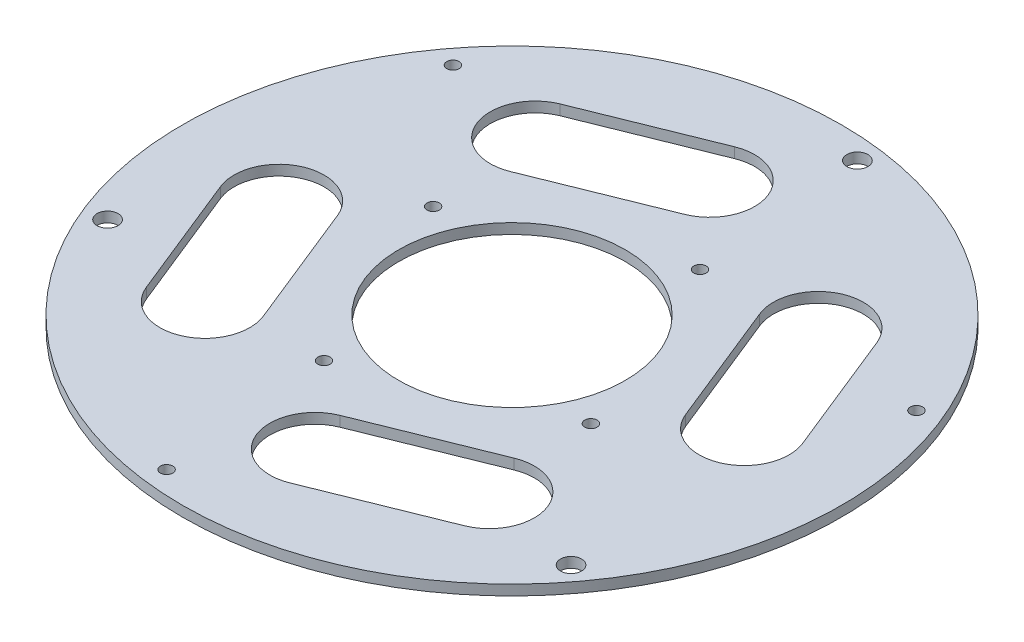
SolidWorks part; units mm, degrees
material "Aleación 1060"
ref_plane "Front Plane" through (0, 0, 0) normal (0, 0, 1) x (1, 0, 0)
ref_plane "Top Plane" through (0, 0, 0) normal (0, 1, 0) x (1, 0, 0)
ref_plane "Right Plane" through (0, 0, 0) normal (1, 0, 0) x (0, 0, -1)
sketch "Sketch1" plane through (0, 0, 0) normal (0, 1, 0) x (1, 0, 0)
  circle A0 centre (0, 0) radius 160
  circle A1 centre (0, 0) radius 55
  dimension "D1" = 0
extrude "Boss-Extrude1" add sketch "Sketch1" along normal blind 3
sketch "Sketch2" plane through (0, 3, 0) normal (0, 1, 0) x (1, 0, 0)
  circle A1 centre (0, 0) radius 70
  circle A2 centre (64.7949, -26.4882) radius 2.5
  dimension "D1" = 0
  dimension "D2" = 70
extrude "Cut-Extrude1" cut sketch "Sketch2" against normal blind 5 contours A2
pattern_circular "CirPattern1" count 4 over 360 about axis through (0, 0, 0) along (0, 1, 0) of "Cut-Extrude1"
sketch "Sketch3" plane through (0, 0, 0) normal (0, -1, 0) x (1, 0, 0)
  line L0 (64.7949, 26.4882) -> (26.4882, -64.7949)
  line L3 (45.6406, -19.1556) -> (138.3138, -58.0457)
  line L4 (138.3138, -58.0457) -> (64.7949, 26.4882)
  circle A0 centre (0, 0) radius 140
  circle A1 centre (138.3138, -58.0457) radius 5.1
  circle A2 centre (64.7949, 26.4882) radius 2.5 construction
  circle A6 centre (26.4882, -64.7949) radius 2.5 construction
  point P11 (45.6406, -19.1556)
  dimension "D1" = 0
  dimension "D2" = 10.2
  dimension "D4" = 0
  dimension "D14" = 150
  dimension "D3" = 0
  dimension "D5" = 0
  dimension "D6" = 0
  dimension "D7" = 0
  dimension "D8" = 49.495
  dimension "D9" = 0
  dimension "D10" = 0
  dimension "D11" = 0
  dimension "D12" = 90
  dimension "D13" = 0
extrude "Cut-Extrude3" cut sketch "Sketch3" against normal through all contours A0 A1 L4 L3 | L4 A1 L3
pattern_circular "CirPattern2" count 3 over 360 about axis through (0, 0, 0) along (0, 1, 0) of "Cut-Extrude3"
sketch "Sketch4" plane through (0, 3, 0) normal (0, 1, 0) x (1, 0, 0)
  line L0 (78.13, -76.3093) -> (-0.703, -108.0953) construction
  line L1 (87.4788, -99.4955) -> (8.6458, -131.2815)
  line L2 (68.7812, -53.1231) -> (-10.0519, -84.9091)
  arc A0 (87.4788, -99.4955) -> (68.7812, -53.1231) centre (78.13, -76.3093) ccw
  arc A1 (-10.0519, -84.9091) -> (8.6458, -131.2815) centre (-0.703, -108.0953) ccw
  point P2 (38.7135, -92.2023)
  dimension "D1" = 25
  dimension "D2" = 85
  dimension "D3" = 100
extrude "Cut-Extrude4" cut sketch "Sketch4" against normal through all
pattern_circular "CirPattern3" count 4 over 360 about axis through (0, 0, 0) along (0, 1, 0) of "Cut-Extrude4"
sketch "Sketch5" plane through (0, 3, 0) normal (0, 1, 0) x (1, 0, 0)
  circle A1 centre (0, 0) radius 160
extrude "Boss-Extrude2" add sketch "Sketch5" along normal blind 5 contours A1
sketch "Sketch6" plane through (0, 3, 0) normal (0, -1, 0) x (-1, 0, 0)
  circle A0 centre (-138.3138, 58.0457) radius 5.1
extrude "Cut-Extrude5" cut sketch "Sketch6" against normal blind 5
sketch "Sketch7" plane through (0, 3, 0) normal (0, -1, 0) x (-1, 0, 0)
  circle A0 centre (119.4259, 90.7604) radius 5.1
extrude "Cut-Extrude6" cut sketch "Sketch7" against normal blind 5
sketch "Sketch8" plane through (0, 3, 0) normal (0, -1, 0) x (-1, 0, 0)
  circle A0 centre (18.8878, -148.8061) radius 5.1
extrude "Cut-Extrude7" cut sketch "Sketch8" against normal blind 5
sketch "Sketch9" plane through (0, 3, 0) normal (0, -1, 0) x (-1, 0, 0)
  circle A0 centre (26.4882, -64.7949) radius 2.5
extrude "Cut-Extrude8" cut sketch "Sketch9" against normal blind 5
sketch "Sketch10" plane through (0, 3, 0) normal (0, -1, 0) x (-1, 0, 0)
  circle A0 centre (-64.7949, -26.4882) radius 2.5
extrude "Cut-Extrude9" cut sketch "Sketch10" against normal blind 5 contours A0
sketch "Sketch11" plane through (0, 3, 0) normal (0, -1, 0) x (-1, 0, 0)
  circle A0 centre (64.7949, 26.4882) radius 2.5
extrude "Cut-Extrude10" cut sketch "Sketch11" against normal blind 5 contours A0
sketch "Sketch12" plane through (0, 3, 0) normal (0, -1, 0) x (-1, 0, 0)
  circle A0 centre (-26.4882, 64.7949) radius 2.5
extrude "Cut-Extrude11" cut sketch "Sketch12" against normal blind 5
sketch "Sketch13" plane through (0, 3, 0) normal (0, -1, 0) x (-1, 0, 0)
  circle A1 centre (0, 0) radius 55
extrude "Cut-Extrude12" cut sketch "Sketch13" against normal blind 5
sketch "Sketch14" plane through (0, 3, 0) normal (0, -1, 0) x (-1, 0, 0)
  line L0 (16.7984, 124.7596) -> (77.0825, 100.4527)
  line L1 (-59.645, 60.6286) -> (-83.9519, 0.3445)
  line L4 (-100.1136, 77.0825) -> (-124.468, 16.6808)
  line L5 (84.291, -0.3445) -> (59.9367, -60.7462)
  line L6 (124.7596, -16.7984) -> (100.4527, -77.0825)
  line L7 (-115.3885, 48.0623) -> (-112.3145, 46.8228)
  line L8 (131.2815, -8.6458) -> (99.4955, -87.4788) construction
  line L9 (-69.0161, 29.3647) -> (-71.7985, 30.4865)
  line L10 (-53.1231, 68.7812) -> (-84.9091, -10.0519) construction
  line L11 (-131.2815, 8.6458) -> (-99.4955, 87.4788) construction
  line L12 (115.3885, -48.0623) -> (112.6062, -46.9404)
  line L13 (-48.0623, -115.3885) -> (-46.8228, -112.3145)
  line L14 (48.0623, 115.3885) -> (46.9404, 112.6062)
  line L15 (-29.3647, -69.0161) -> (-30.4865, -71.7985)
  line L16 (-77.0825, -100.1136) -> (-16.6808, -124.468)
  line L17 (-60.6286, -59.645) -> (-0.3445, -83.9519)
  line L18 (0.3445, 84.291) -> (60.7462, 59.9367)
  line L19 (48.0623, 115.3885) -> (46.9404, 112.6062)
  line L20 (8.6458, 131.2815) -> (87.4788, 99.4955) construction
  arc A1 (-124.468, 16.6808) -> (-83.9519, 0.3445) centre (-104.2099, 8.5126) ccw
  arc A3 (59.9367, -60.7462) -> (100.4527, -77.0825) centre (80.1947, -68.9143) ccw
  arc A5 (-59.645, 60.6286) -> (-100.161, 76.9649) centre (-79.8793, 68.8555) ccw
  arc A6 (124.7596, -16.7984) -> (84.2436, -0.4621) centre (104.5253, -8.5714) ccw
  arc A7 (-16.6808, -124.468) -> (-0.3445, -83.9519) centre (-8.5126, -104.2099) ccw
  arc A8 (-60.6286, -59.645) -> (-76.9649, -100.161) centre (-68.8555, -79.8793) ccw
  arc A9 (16.7984, 124.7596) -> (0.4621, 84.2436) centre (8.5714, 104.5253) ccw
  arc A10 (60.7462, 59.9367) -> (77.0825, 100.4527) centre (68.9143, 80.1947) ccw
extrude "Cut-Extrude15" cut sketch "Sketch14" against normal blind 5 contours L17 A8 L16 A7 | L6 A6 L5 A3 | L1 A5 L4 A1 | L18 A10 L0 A9
sketch "Sketch15" plane through (0, 0, 0) normal (0, -1, 0) x (1, 0, 0)
  circle A0 centre (0, 0) radius 160
extrude "Cut-Extrude16" cut sketch "Sketch15" against normal blind 3
sketch "Sketch16" plane through (0, 3, 0) normal (0, -1, 0) x (-1, 0, 0)
  line L3 (-65.9454, 16.8302) -> (-58.206, 35.272)
  line L4 (-58.206, 35.272) -> (-12.1014, 15.9235)
  line L5 (47.5481, 48.6953) -> (59.6495, 32.7718)
  line L6 (-65.9454, 16.8302) -> (-19.8408, -2.5184)
  line L7 (18.3973, -65.5255) -> (-1.4435, -68.0439)
  line L8 (18.3973, -65.5255) -> (12.1014, -15.9235)
  line L9 (-1.4435, -68.0439) -> (-7.7394, -18.4418)
  line L10 (47.5481, 48.6953) -> (7.7394, 18.4418)
  line L11 (59.6495, 32.7718) -> (19.8408, 2.5184)
  arc A0 (-19.8408, -2.5184) -> (-7.7394, -18.4418) centre (0, 0) ccw
  arc A1 (12.1014, -15.9235) -> (19.8408, 2.5184) centre (0, 0) ccw
  arc A2 (7.7394, 18.4418) -> (-12.1014, 15.9235) centre (0, 0) ccw
extrude "Boss-Extrude4" add sketch "Sketch16" along normal blind 14
sketch "Sketch20" plane through (0, 3, 0) normal (0, 1, 0) x (1, 0, 0)
  circle A0 centre (0, 0) radius 18
extrude "Cut-Extrude19" cut sketch "Sketch20" against normal blind 13
sketch "Sketch21" plane through (0, -11, 0) normal (0, -1, 0) x (1, 0, 0)
  line L1 (-48.1531, -47.8991) -> (-59.0444, -33.568)
  line L4 (1.4435, 68.0439) -> (-18.3973, 65.5255) construction
  line L9 (-48.1531, -47.8991) -> (1.3086, -10.3096)
  line L10 (-59.0444, -33.568) -> (-9.5827, 4.0215)
  line L11 (58.5929, -34.3499) -> (65.5584, -17.7523)
  line L12 (-17.4053, 65.6514) -> (0.4514, 67.9179)
  line L15 (8.2741, 6.2881) -> (65.5584, -17.7523)
  line L16 (8.2741, 6.2881) -> (0.4514, 67.9179)
  line L17 (1.3086, -10.3096) -> (58.5929, -34.3499)
  line L18 (-9.5827, 4.0215) -> (-17.4053, 65.6514)
extrude "Cut-Extrude21" cut sketch "Sketch21" against normal blind 14
sketch "Sketch22" plane through (0, -11, 0) normal (0, -1, 0) x (-1, 0, 0)
  line L0 (12.1014, -15.9235) -> (18.3973, -65.5255)
  line L1 (18.3973, -65.5255) -> (-1.4435, -68.0439)
  line L2 (-1.4435, -68.0439) -> (-7.6534, -19.1196)
  line L3 (-7.7394, -18.4418) -> (-1.4435, -68.0439) construction
  line L4 (-19.8408, -2.5184) -> (-65.9454, 16.8302)
  line L5 (-65.9454, 16.8302) -> (-58.206, 35.272)
  line L6 (-58.206, 35.272) -> (-12.1014, 15.9235)
  line L7 (7.7394, 18.4418) -> (47.5481, 48.6953)
  line L8 (47.5481, 48.6953) -> (7.7394, 18.4418) construction
  line L9 (47.5481, 48.6953) -> (37.0089, 40.6859) construction
  line L10 (47.5481, 48.6953) -> (59.6495, 32.7718)
  line L11 (59.6495, 32.7718) -> (19.8408, 2.5184)
  line L18 (-0.4514, -67.9179) -> (-8.2741, -6.2881)
  line L19 (-8.2741, -6.2881) -> (-65.5584, 17.7523)
  line L20 (-65.5584, 17.7523) -> (-65.9454, 16.8302)
  line L21 (-65.9454, 16.8302) -> (-19.8408, -2.5184)
  line L22 (-7.7394, -18.4418) -> (-1.4435, -68.0439)
  line L23 (-1.4435, -68.0439) -> (-0.4514, -67.9179)
  line L28 (-7.7394, -18.4418) -> (-7.6534, -19.1196)
  arc A0 (12.1014, -15.9235) -> (19.8408, 2.5184) centre (0, 0) ccw
  arc A1 (7.7394, 18.4418) -> (-12.1014, 15.9235) centre (0, 0) ccw
  arc A3 (-19.8408, -2.5184) -> (-7.7394, -18.4418) centre (0, 0) ccw
  arc A4 (-19.8408, -2.5184) -> (-7.7394, -18.4418) centre (0, 0) ccw
  dimension "D1" = 0
extrude "Cut-Extrude24" add sketch "Sketch22" along normal blind 14
sketch "Sketch23" plane through (0, 8, 0) normal (0, 1, 0) x (1, 0, 0)
  circle A0 centre (-119.4259, 90.7604) radius 5.1
  circle A1 centre (138.3138, 58.0457) radius 5.1
  circle A2 centre (-18.8878, -148.8061) radius 5.1
  circle A4 centre (-138.3138, -58.0457) radius 5.1
  circle A5 centre (18.8878, 148.8061) radius 5.1
  circle A6 centre (119.4259, -90.7604) radius 5.1
extrude "Cut-Extrude22" cut sketch "Sketch23" against normal blind 5
sketch "Sketch24" plane through (0, 8, 0) normal (0, 1, 0) x (1, 0, 0)
  circle A0 centre (64.7949, -26.4882) radius 3
  circle A1 centre (-26.4882, -64.7949) radius 3
  circle A2 centre (-64.7949, 26.4882) radius 3
  circle A3 centre (26.4882, 64.7949) radius 3
extrude "Cut-Extrude23" cut sketch "Sketch24" against normal blind 10 contours A1 | A0 | A3 | A2
sketch "Sketch25" plane through (0, 8, 0) normal (0, 1, 0) x (1, 0, 0)
  circle A0 centre (-119.4259, 90.7604) radius 3
  circle A1 centre (138.3138, 58.0457) radius 3
  circle A2 centre (-18.8878, -148.8061) radius 3
  circle A3 centre (-119.4259, 90.7604) radius 5.1
  circle A5 centre (138.3138, 58.0457) radius 5.1
  circle A6 centre (-18.8878, -148.8061) radius 5.1
extrude "Boss-Extrude6" add sketch "Sketch25" against normal blind 5
sketch "Sketch26" plane through (0, 3, 0) normal (0, -1, 0) x (-1, 0, 0)
  line L0 (64.9579, -16.4157) -> (57.2184, -34.8576)
  line L1 (-46.6954, -48.0473) -> (-58.7968, -32.1238)
  line L2 (1.5783, 66.9814) -> (-18.2625, 64.463)
  line L3 (-7.7394, -18.4418) -> (-46.6954, -48.0473)
  line L4 (1.5783, 66.9814) -> (7.7394, 18.4418)
  line L5 (57.2184, -34.8576) -> (12.1014, -15.9235)
  line L6 (64.9579, -16.4157) -> (19.8408, 2.5184)
  line L7 (-19.8408, -2.5184) -> (-58.7968, -32.1238)
  line L8 (-18.2625, 64.463) -> (-12.1014, 15.9235)
  line L9 (4.1767, 70.3353) -> (-21.6164, 67.0614)
  line L10 (-21.6164, 67.0614) -> (-15.2857, 17.1857)
  line L11 (-22.9722, -1.1301) -> (-63.0005, -31.5505)
  line L12 (-47.2687, -52.251) -> (-63.0005, -31.5505)
  line L13 (-7.2404, -21.8306) -> (-47.2687, -52.251)
  line L14 (58.8238, -38.7848) -> (12.4648, -19.3295)
  line L15 (68.885, -14.8104) -> (58.8238, -38.7848)
  line L16 (68.885, -14.8104) -> (22.5261, 4.6449)
  line L17 (4.1767, 70.3353) -> (10.5074, 20.4596)
  arc A0 (19.8408, 2.5184) -> (7.7394, 18.4418) centre (0, 0) ccw
  arc A1 (-7.7394, -18.4418) -> (12.1014, -15.9235) centre (0, 0) ccw
  arc A2 (-12.1014, 15.9235) -> (-19.8408, -2.5184) centre (0, 0) ccw
  arc A4 (-15.2857, 17.1857) -> (-22.9722, -1.1301) centre (0, 0) ccw
  arc A5 (-7.2404, -21.8306) -> (12.4648, -19.3295) centre (0, 0) ccw
  arc A6 (22.5261, 4.6449) -> (10.5074, 20.4596) centre (0, 0) ccw
  point P8 (6.0507, -7.9617)
  point P9 (-113.3752, -98.7221)
  point P10 (-8.9674, 150.0653)
  point P11 (9.9204, 1.2592)
  point P12 (134.4441, -67.2666)
  point P13 (-3.8697, -9.2209)
  point P14 (142.1835, -48.8248)
  point P15 (3.8697, 9.2209)
  point P16 (-6.0507, 7.9617)
  point P17 (-125.4766, -82.7987)
  point P18 (-28.8083, 147.5469)
  point P19 (-9.9204, -1.2592)
  dimension "D1" = 3
extrude "Boss-Extrude7" add sketch "Sketch26" along normal blind 12
sketch "Sketch27" plane through (0, -9, 0) normal (0, -1, 0) x (1, 0, 0)
  line L0 (-4.1767, -70.3353) -> (21.6164, -67.0614)
  line L1 (21.6164, -67.0614) -> (15.2857, -17.1857)
  line L2 (-10.5074, -20.4596) -> (-4.1767, -70.3353)
  line L3 (-22.5261, -4.6449) -> (-68.885, 14.8104)
  line L4 (-68.885, 14.8104) -> (-58.8238, 38.7848)
  line L5 (-58.8238, 38.7848) -> (-12.4648, 19.3295)
  line L6 (47.2687, 52.251) -> (7.2404, 21.8306)
  line L7 (47.2687, 52.251) -> (63.0005, 31.5505)
  line L8 (63.0005, 31.5505) -> (22.9722, 1.1301)
  arc A0 (-22.5261, -4.6449) -> (-10.5074, -20.4596) centre (0, 0) ccw
  arc A1 (7.2404, 21.8306) -> (-12.4648, 19.3295) centre (0, 0) ccw
  arc A2 (15.2857, -17.1857) -> (22.9722, 1.1301) centre (0, 0) ccw
extrude "Boss-Extrude8" add sketch "Sketch27" along normal blind 2
sketch "Sketch28" plane through (8.7198, 0, -68.6983) normal (0.1259, 0, -0.992) x (-0.992, 0, -0.1259)
  line L0 (-13, 3) -> (-13, -11)
  line L1 (-13, -11) -> (13, -11)
  line L2 (13, -11) -> (13, 3)
  line L3 (13, 3) -> (-13, 3)
  line L4 (11, 1) -> (-11, 1)
  line L5 (-11, 1) -> (-11, -9)
  line L6 (-11, -9) -> (11, -9)
  line L7 (11, -9) -> (11, 1)
  dimension "D1" = 2
extrude "Cut-Extrude25" cut sketch "Sketch28" against normal blind 15 contours L4 L5 L6 L7
sketch "Sketch29" plane through (-63.8544, 0, 26.7976) normal (-0.9221, 0, 0.387) x (0.387, 0, 0.9221)
  line L0 (-13, -11) -> (13, -11)
  line L2 (13, -11) -> (13, 3)
  line L3 (13, 3) -> (-13, 3)
  line L4 (-13, 3) -> (-13, -11)
  line L5 (-11, 1) -> (-11, -9)
  line L6 (-11, -9) -> (11, -9)
  line L7 (11, -9) -> (11, 1)
  line L8 (11, 1) -> (-11, 1)
  dimension "D1" = 2
extrude "Cut-Extrude26" cut sketch "Sketch29" against normal blind 15 contours L5 L6 L7 L8
sketch "Sketch30" plane through (55.1346, 0, 41.9008) normal (0.7962, 0, 0.6051) x (0.6051, 0, -0.7962)
  line L0 (-13, -11) -> (13, -11)
  line L1 (13, -11) -> (13, 3)
  line L2 (13, 3) -> (-13, 3)
  line L3 (-13, 3) -> (-13, -11)
  line L4 (-11, 1) -> (-11, -9)
  line L5 (-11, -9) -> (11, -9)
  line L6 (11, -9) -> (11, 1)
  line L7 (11, 1) -> (-11, 1)
  dimension "D1" = 2
extrude "Cut-Extrude27" cut sketch "Sketch30" against normal blind 15 contours L4 L5 L6 L7
sketch "Croquis1" plane through (0, 3, 0) normal (0, -1, 0) x (1, 0, 0)
  circle A0 centre (0, 0) radius 160
extrude "Cortar-Extruir1" cut sketch "Croquis1" along normal through all
sketch "Croquis2" plane through (0, 3, 0) normal (0, -1, 0) x (-1, 0, 0)
  line L0 (0, 0) -> (-138.3138, 58.0457) construction
  line L1 (0, 0) -> (-64.7949, -26.4882) construction
  line L2 (0, 0) -> (26.4882, -64.7949) construction
  line L3 (0, 0) -> (-119.4259, -90.7604) construction
  line L4 (0, 0) -> (119.4259, 90.7604) construction
  line L5 (0, 0) -> (242.2793, 0) construction
  dimension "D2" = 120
  dimension "D1" = 45.001
  dimension "D3" = 60
